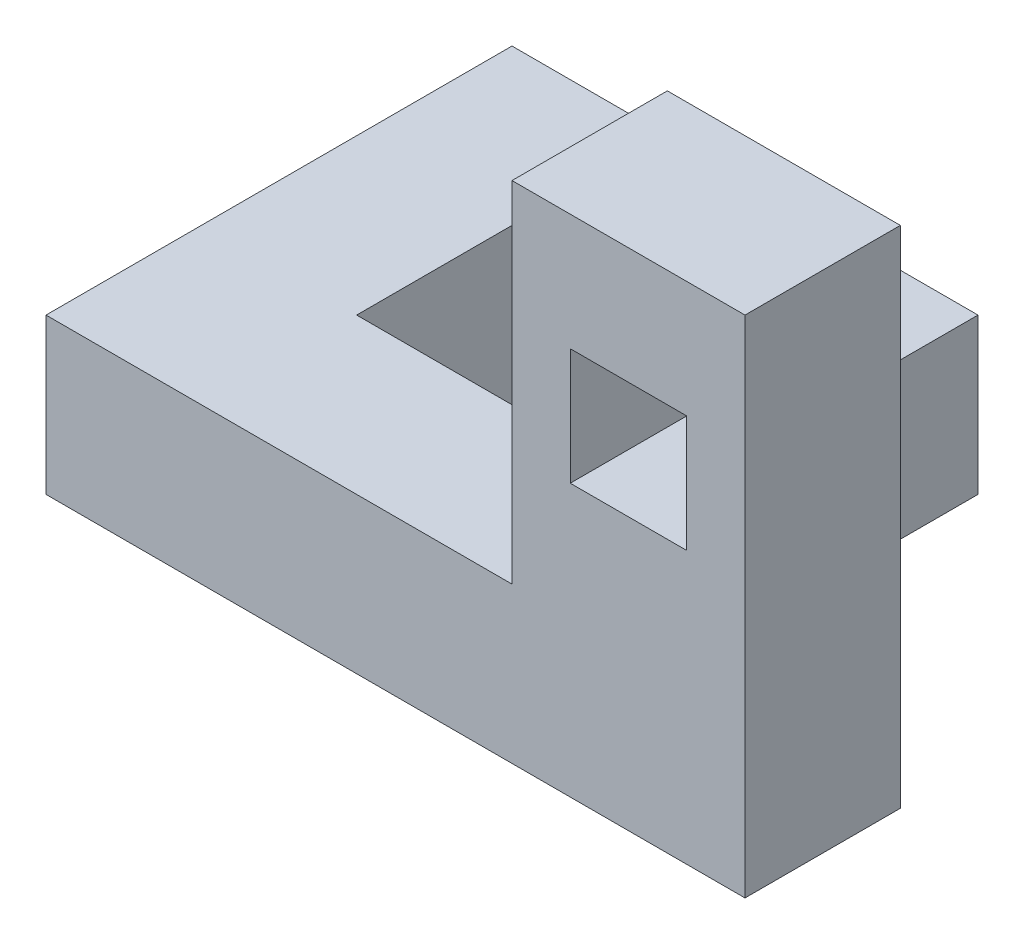
SolidWorks part; units mm, degrees
ref_plane "Front Plane" through (0, 0, 0) normal (0, 0, 1) x (1, 0, 0)
ref_plane "Top Plane" through (0, 0, 0) normal (0, 1, 0) x (1, 0, 0)
ref_plane "Right Plane" through (0, 0, 0) normal (1, 0, 0) x (0, 0, -1)
sketch "Sketch1" plane through (0, 0, 0) normal (0, 1, 0) x (1, 0, 0)
  line L1 (-30, -30) -> (30, -30)
  line L2 (-30, -30) -> (-30, 30)
  line L3 (-30, 30) -> (30, 30)
  line L4 (30, -30) -> (30, 30)
  line L5 (-30, -30) -> (30, 30) construction
  line L6 (-30, 30) -> (30, -30) construction
  line L7 (-10, -10) -> (10, -10)
  line L8 (-10, -10) -> (-10, 10)
  line L9 (-10, 10) -> (10, 10)
  line L10 (10, -10) -> (10, 10)
  line L11 (-10, -10) -> (10, 10) construction
  line L12 (-10, 10) -> (10, -10) construction
  point P0 (0, 0)
  point P6 (0, 0)
  dimension "D1" = 60
  dimension "D2" = 60
  dimension "D3" = 20
  dimension "D4" = 20
extrude "Boss-Extrude1" add sketch "Sketch1" along normal blind 20
sketch "Sketch2" plane through (0, 0, 30) normal (0, 0, 1) x (1, 0, 0)
  line L0 (45, 65) -> (45, 0) construction
  line L1 (30, 0) -> (60, 0)
  line L2 (30, 0) -> (30, 65)
  line L3 (30, 65) -> (60, 65)
  line L4 (60, 0) -> (60, 65)
  line L6 (37.5, 35) -> (52.5, 35)
  line L7 (37.5, 35) -> (37.5, 50)
  line L8 (37.5, 50) -> (52.5, 50)
  line L9 (52.5, 35) -> (52.5, 50)
  line L10 (37.5, 35) -> (52.5, 50) construction
  line L11 (37.5, 50) -> (52.5, 35) construction
  point P7 (45, 42.5)
  dimension "D1" = 30
  dimension "D2" = 65
  dimension "D3" = 15
  dimension "D4" = 15
  dimension "D5" = 15
extrude "Boss-Extrude2" add sketch "Sketch2" against normal blind 20
